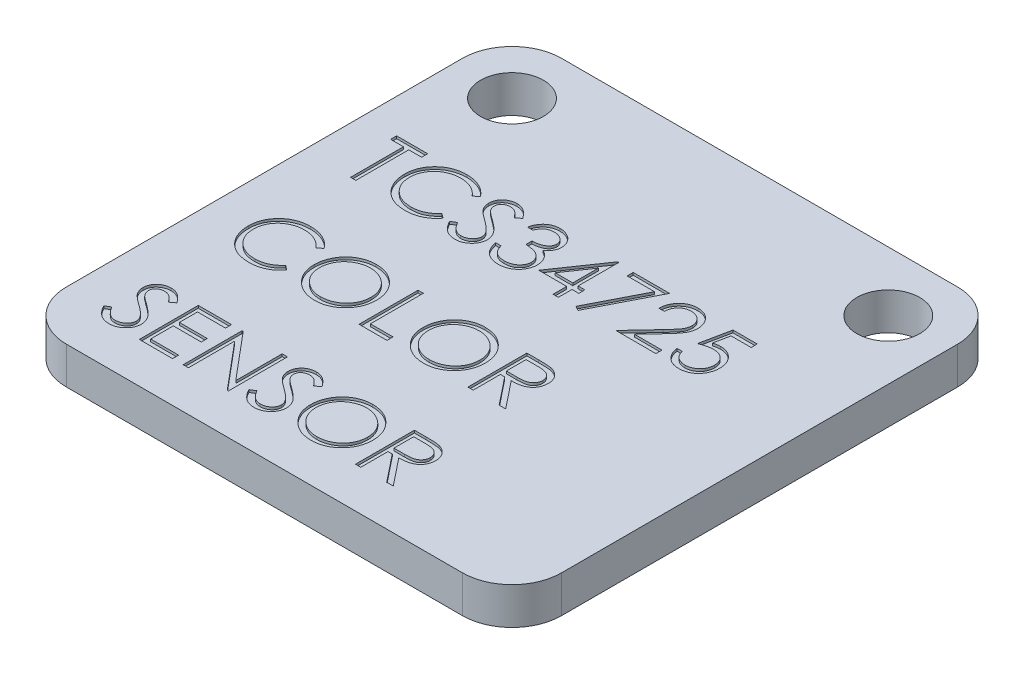
SolidWorks part; units mm, degrees
ref_plane "Front Plane" through (0, 0, 0) normal (0, 0, 1) x (1, 0, 0)
ref_plane "Top Plane" through (0, 0, 0) normal (0, 1, 0) x (1, 0, 0)
ref_plane "Right Plane" through (0, 0, 0) normal (1, 0, 0) x (0, 0, -1)
sketch "Sketch1" plane through (0, 0, 0) normal (0, 1, 0) x (1, 0, 0)
  line L0 (-7.6, 7.6) -> (7.6, 7.6) construction
  line L1 (-8, -10) -> (8, -10)
  line L2 (-10, -8) -> (-10, 8)
  line L3 (-8, 10) -> (8, 10)
  line L4 (10, -8) -> (10, 8)
  line L5 (-10, -10) -> (10, 10) construction
  line L6 (-10, 10) -> (10, -10) construction
  circle A0 centre (-7.6, 7.6) radius 1.27
  circle A1 centre (7.6, 7.6) radius 1.27
  arc A2 (-8, 10) -> (-10, 8) centre (-8, 8) ccw
  arc A3 (10, 8) -> (8, 10) centre (8, 8) ccw
  arc A4 (-8, -10) -> (-10, -8) centre (-8, -8) cw
  arc A5 (10, -8) -> (8, -10) centre (8, -8) cw
  point P0 (0, 0)
  dimension "D4" = 2.54
  dimension "D5" = 2.54
  dimension "D6" = 2
  dimension "D7" = 2
  dimension "D8" = 2
  dimension "D9" = 2
  dimension "D1" = 20
  dimension "D2" = 20
  dimension "D3" = 15.2
extrude "Boss-Extrude1" add sketch "Sketch1" along normal blind 1.5
sketch "Sketch2" plane through (0, 1.5, 0) normal (0, 1, 0) x (1, 0, 0)
  text T0 "TCS34725\r\nCOLOR\r\nSENSOR" font "Century Gothic" height in points 9
extrude "Cut-Extrude1" cut sketch "Sketch2" against normal blind 0.1
sketch "Sketch3" plane through (0, 0, 0) normal (0, -1, 0) x (1, 0, 0)
  line L0 (8, -10) -> (-8, -10) construction
  line L1 (2, -1.5) -> (4, -1.5)
  line L2 (2, -1.5) -> (2, 1.5)
  line L3 (2, 1.5) -> (4, 1.5)
  line L4 (4, -1.5) -> (4, 1.5)
  line L5 (10, 8) -> (10, -8) construction
  dimension "D1" = 3
  dimension "D2" = 2
  dimension "D3" = 8.5
  dimension "D4" = 6
extrude "Boss-Extrude2" add sketch "Sketch3" along normal blind 1
